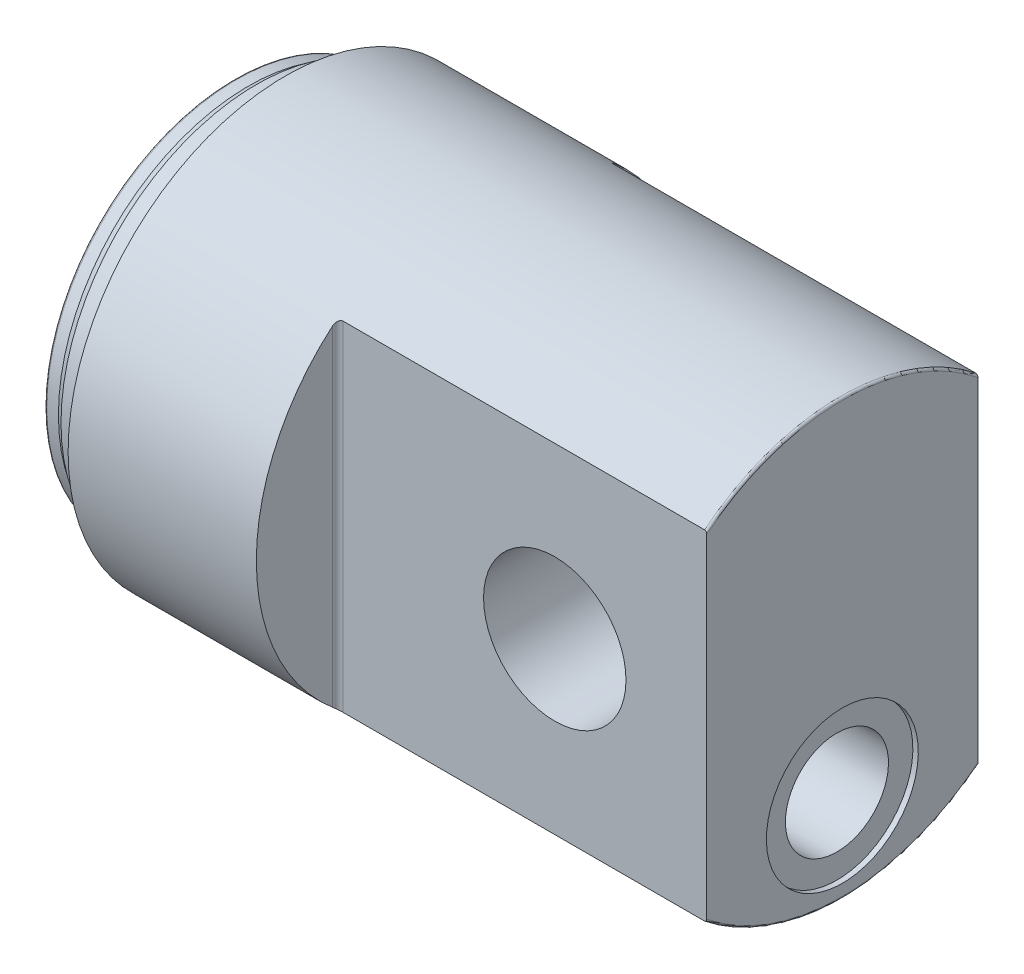
SolidWorks part; units mm, degrees
ref_plane "Front" through (0, 0, 0) normal (0, 0, 1) x (1, 0, 0)
ref_plane "Top" through (0, 0, 0) normal (0, 1, 0) x (1, 0, 0)
ref_plane "Right" through (0, 0, 0) normal (1, 0, 0) x (0, 0, -1)
sketch "Sketch1" plane through (0, 0, 0) normal (0, 0, 1) x (1, 0, 0)
  line L0 (-90.5735, 0) -> (40.2132, 0) construction
  line L1 (0, 29.3109) -> (0, -40.3919) construction
  line L2 (28, 0) -> (28, 39.6)
  line L3 (-81.4773, 35) -> (-80.5816, 34.5436)
  line L7 (27.6, 40) -> (-74.6906, 40)
  line L8 (-74.6906, 40) -> (-77, 36)
  line L9 (-77, 36) -> (-80, 36)
  line L10 (-80, 36) -> (-80, 34.9)
  line L11 (-81.4773, 35) -> (-83.6, 35)
  line L12 (-84, 34.6) -> (-84, 25)
  line L13 (28, 0) -> (-32.5662, 0)
  line L14 (-84, 25) -> (-47, 25)
  line L15 (-47, 25) -> (-32.5662, 0)
  circle A0 centre (0, 0) radius 13.125 construction
  arc A1 (27.6, 40) -> (28, 39.6) centre (27.6, 39.6) cw
  arc A2 (-80, 34.9) -> (-80.5816, 34.5436) centre (-80.4, 34.9) cw
  arc A3 (-83.6, 35) -> (-84, 34.6) centre (-83.6, 34.6) ccw
  dimension "D1" = 26.25
  dimension "D16" = 69
  dimension "D17" = 84
  dimension "D6" = 0.4
  dimension "D7" = 0.4
  dimension "D5" = 0.4
  dimension "D2" = 28
  dimension "D3" = 112
  dimension "D4" = 27
  dimension "D8" = 60
  dimension "D9" = 37
  dimension "D10" = 80
  dimension "D11" = 7
  dimension "D12" = 4
  dimension "D13" = 70
  dimension "D14" = 72
  dimension "D15" = 60
  dimension "D20" = 50
revolve "Base-Revolve" add sketch "Sketch1" angle 360 about L0
sketch "Sketch2" plane through (0, 0, 0) normal (0, 0, 1) x (1, 0, 0)
  circle A0 centre (0, 0) radius 13.125
  circle A1 centre (0, 0) radius 13.125 construction
extrude "ø26.25 mm hul" cut sketch "Sketch2" against normal mid plane 100
sketch "Sketch3" plane through (0, 0, 0) normal (0, 1, 0) x (1, 0, 0)
  line L0 (0, 0) -> (25, 0) construction
  line L3 (28, 25) -> (-39, 25)
  line L4 (28, 25) -> (28, 40)
  line L5 (28, 40) -> (-40, 40)
  line L6 (-40, 26) -> (-40, 40)
  line L7 (-40, -26) -> (-40, -40)
  line L8 (28, -40) -> (-40, -40)
  line L9 (28, -25) -> (28, -40)
  line L10 (28, -25) -> (-39, -25)
  line L12 (28, -39.6) -> (28, 39.6) construction
  line L13 (-13.125, 40) -> (-74.6906, 40) construction
  arc A0 (-39, 25) -> (-40, 26) centre (-39, 26) cw
  arc A1 (-39, -25) -> (-40, -26) centre (-39, -26) ccw
  dimension "D1" = 1
  dimension "D2" = 50
  dimension "D3" = 40
extrude "Cut-Extrude1" cut sketch "Sketch3" against normal mid plane 100
sketch "Sketch4" plane through (0, 0, 0) normal (0, 0, 1) x (1, 0, 0)
  line L0 (28, -23.5) -> (-84, -23.5) construction
  line L1 (28, -30.7109) -> (28, 30.7109) construction
  line L2 (28, -9.5) -> (27, -9.5)
  line L3 (27, -9.5) -> (27, -14)
  line L4 (27, -14) -> (8, -14)
  line L5 (8, -14) -> (6.2679, -17)
  line L6 (28, -9.5) -> (28, -23.5)
  line L7 (28, -23.5) -> (-55.7528, -23.5)
  line L8 (6.2679, -17) -> (-52, -17)
  line L9 (-52, -17) -> (-55.7528, -23.5)
  line L10 (-84, 35) -> (-84, -35) construction
  dimension "D1" = 23.5
  dimension "D2" = 19
  dimension "D3" = 28
  dimension "D4" = 1
  dimension "D5" = 60
  dimension "D6" = 20
  dimension "D7" = 13
  dimension "D8" = 80
revolve "Cut-Revolve1" cut sketch "Sketch4" angle 360 about L0
cosmetic thread "Cosmetic Thread1" parameters "D1"=16, "D2"=20.992
